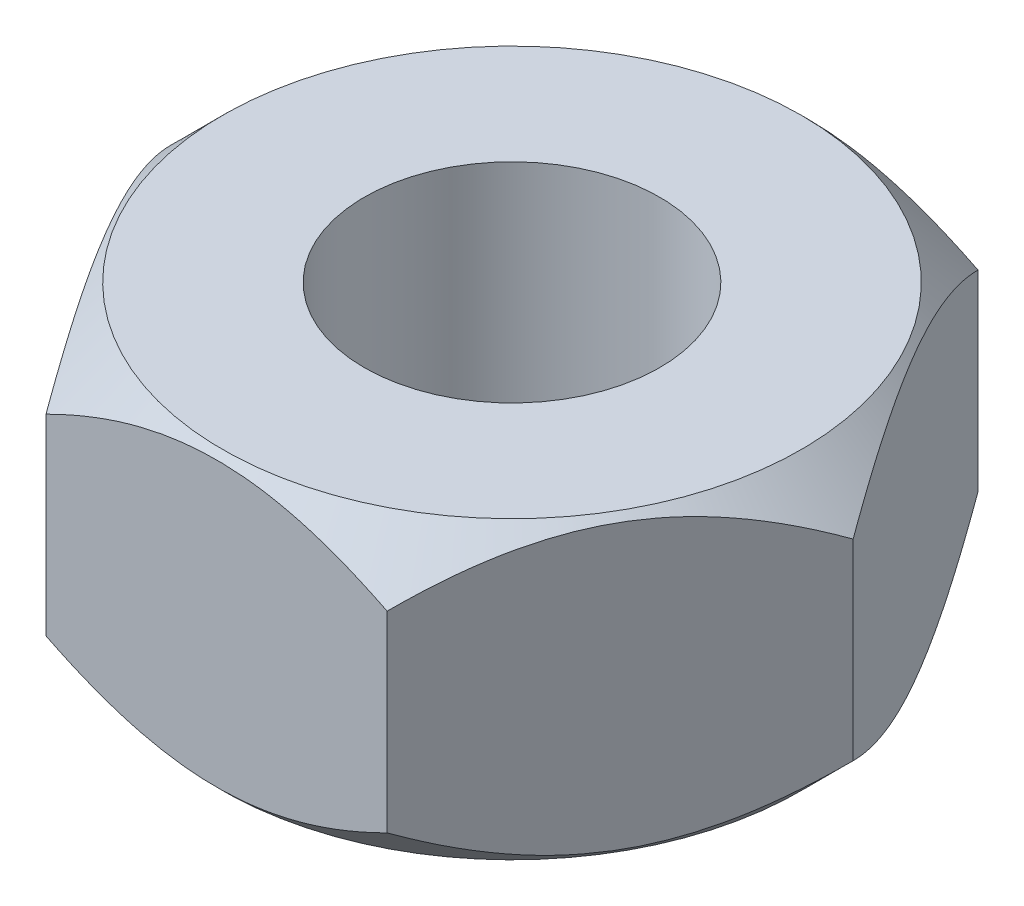
SolidWorks part; units mm, degrees
ref_plane "Front Plane" through (0, 0, 0) normal (0, 0, 1) x (1, 0, 0)
ref_plane "Top Plane" through (0, 0, 0) normal (0, 1, 0) x (1, 0, 0)
ref_plane "Right Plane" through (0, 0, 0) normal (1, 0, 0) x (0, 0, -1)
sketch "Sketch1" plane through (0, 0, 0) normal (0, 1, 0) x (1, 0, 0)
  line L1 (2.3094, 4) -> (-2.3094, 4)
  line L2 (-2.3094, 4) -> (-4.6188, 0)
  line L3 (-4.6188, 0) -> (-2.3094, -4)
  line L4 (-2.3094, -4) -> (2.3094, -4)
  line L5 (2.3094, -4) -> (4.6188, 0)
  line L6 (4.6188, 0) -> (2.3094, 4)
  circle A0 centre (0, 0) radius 2
  circle A1 centre (0, 0) radius 4 construction
  dimension "D1" = 4
  dimension "D2" = 8
extrude "Boss-Extrude1" add sketch "Sketch1" along normal mid plane 4 contours L1 L2 L3 L4 L5 L6
sketch "Sketch2" plane through (0, 0, 0) normal (0, 0, 1) x (1, 0, 0)
  line L0 (-4.6188, 1.3) -> (-3.9188, 2)
  line L1 (-4.6188, 2) -> (-4.6188, -2) construction
  line L2 (-4.6188, 2) -> (-2.3094, 2) construction
  line L3 (0, 0) -> (0, 3.2963) construction
  line L4 (-4.6188, 1.3) -> (-4.6188, 2)
  line L5 (-4.6188, 2) -> (-3.9188, 2)
  dimension "D1" = 45
  dimension "D2" = 0.7
revolve "Cut-Revolve1" cut sketch "Sketch2" angle 360 about L3
mirror "Mirror1" about plane through (0, 0, 0) normal (0, 1, 0) of "Cut-Revolve1"
